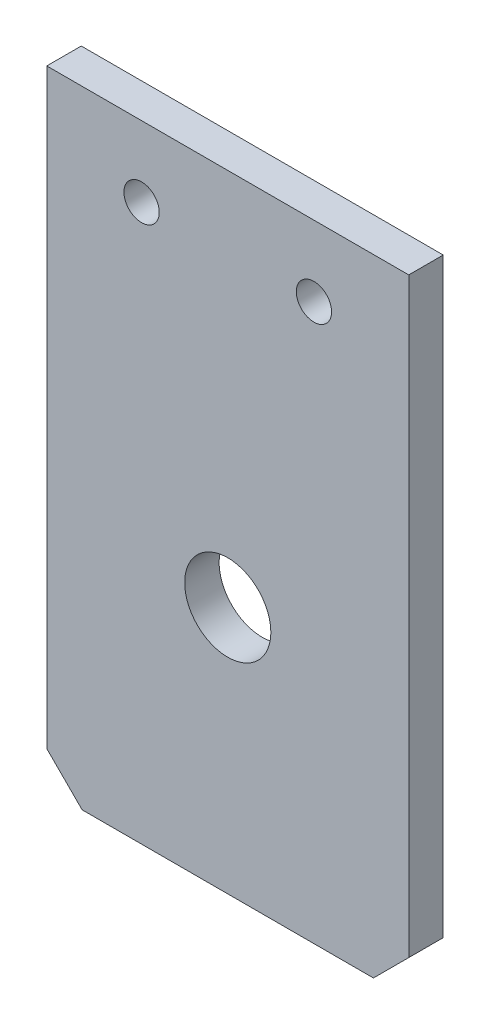
SolidWorks part; units mm, degrees
ref_plane "Alzado" through (0, 0, 0) normal (0, 0, 1) x (1, 0, 0)
ref_plane "Planta" through (0, 0, 0) normal (0, 1, 0) x (1, 0, 0)
ref_plane "Vista lateral" through (0, 0, 0) normal (1, 0, 0) x (0, 0, -1)
sketch "Croquis1" plane through (0, 0, 0) normal (0, 0, 1) x (1, 0, 0)
  line L0 (11, 56.8) -> (31, 56.8) construction
  line L1 (0, 65) -> (42, 65)
  line L2 (0, 65) -> (0, 0)
  line L3 (0, 0) -> (42, 0)
  line L4 (42, 65) -> (42, 0)
  line L5 (21, 56.8) -> (21, 21.08) construction
  line L6 (21, 65) -> (21, 56.8) construction
  line L7 (5.5, 36.58) -> (36.5, 5.58) construction
  line L8 (5.5, 5.58) -> (36.5, 36.58) construction
  circle A0 centre (11, 56.8) radius 2.05
  circle A1 centre (31, 56.8) radius 2.05
  circle A2 centre (5.5, 36.58) radius 1.575 construction
  circle A3 centre (36.5, 36.58) radius 1.575 construction
  circle A4 centre (36.5, 5.58) radius 1.575 construction
  circle A5 centre (5.5, 5.58) radius 1.575 construction
  circle A6 centre (21, 21.08) radius 11.5 construction
  dimension "D3" = 20
  dimension "D8" = 31
  dimension "D11" = 23
  dimension "D4" = 4.1
  dimension "D9" = 3.15
  dimension "D1" = 42
  dimension "D2" = 65
  dimension "D5" = 35.72
  dimension "D6" = 8.2
  dimension "D7" = 31
extrude "Saliente-Extruir1" add sketch "Croquis1" along normal blind 4
sketch "Croquis5" plane through (0, 0, 4) normal (0, 0, 1) x (1, 0, 0)
  line L0 (5.5, 5.58) -> (36.5, 36.58) construction
  circle A0 centre (21, 21.08) radius 5
  dimension "D1" = 10
extrude "Cortar-Extruir2" cut sketch "Croquis5" against normal through all
sketch "Croquis6" plane through (0, 0, 4) normal (0, 0, 1) x (1, 0, 0)
  line L0 (42, 0) -> (42, 65) construction
  line L1 (0, 0) -> (42, 0)
  line L2 (0, 0) -> (0, -7.7)
  line L3 (0, -7.7) -> (42, -7.7)
  line L4 (42, 0) -> (42, -7.7)
  line L5 (0, 0) -> (42, 0) construction
  dimension "D1" = 7.7
extrude "Saliente-Extruir2" add sketch "Croquis6" against normal through all
chamfer "Chaflán1" distance 4.1 angle 45 2 edges at (42, -7.7, 2) (0, -7.7, 2)
